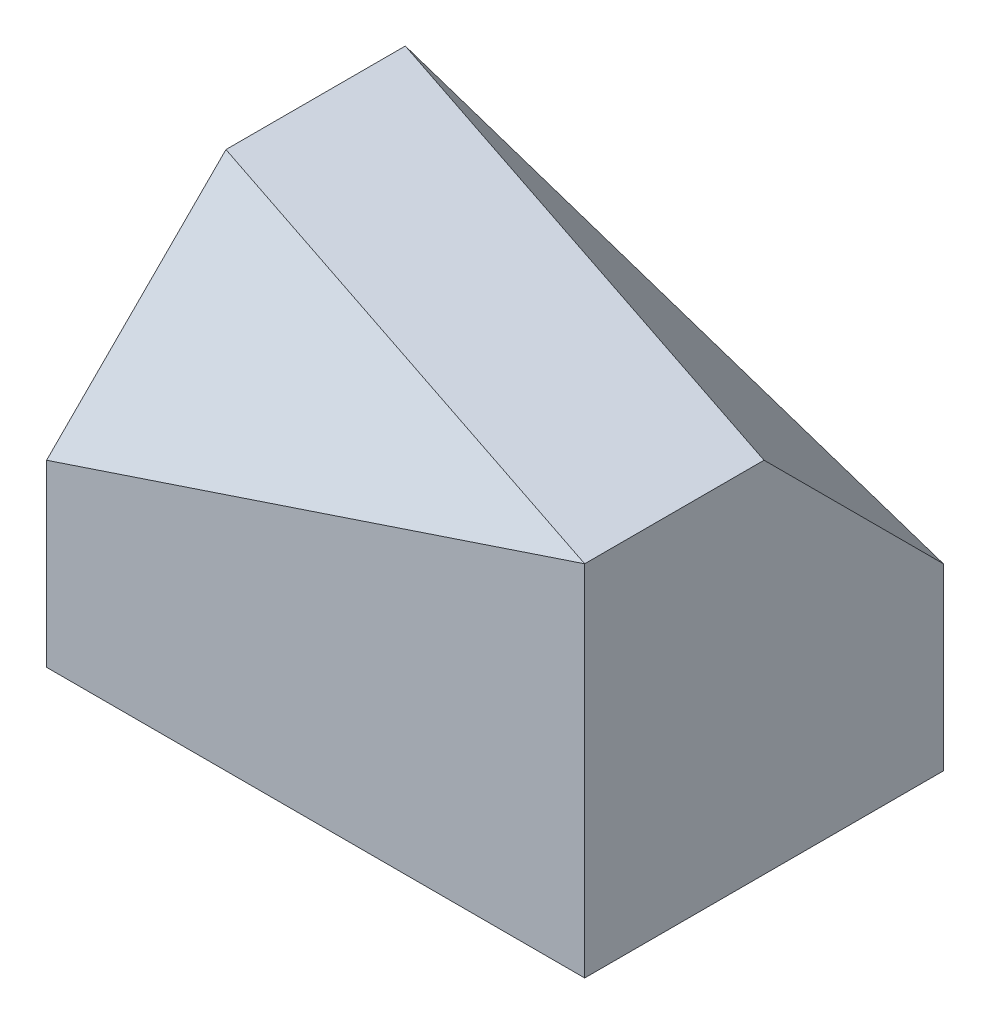
SolidWorks part; units mm, degrees
ref_plane "Front Plane" through (0, 0, 0) normal (0, 0, 1) x (1, 0, 0)
ref_plane "Top Plane" through (0, 0, 0) normal (0, 1, 0) x (1, 0, 0)
ref_plane "Right Plane" through (0, 0, 0) normal (1, 0, 0) x (0, 0, -1)
sketch "Sketch1" plane through (0, 0, 0) normal (0, 1, 0) x (1, 0, 0)
  line L0 (0, 0) -> (0, 1016)
  line L1 (0, 1016) -> (1524, 1016)
  line L2 (1524, 1016) -> (1524, 0)
  line L3 (1524, 0) -> (0, 0)
  line L4 (0, 1016) -> (1524, 508)
  line L5 (1524, 0) -> (0, 508)
  point P6 (1524, 575.0148)
  point P8 (0, 0)
  point P9 (1524, 508)
  dimension "D1" = 1524
  dimension "D2" = 1016
extrude "Boss-Extrude1" add sketch "Sketch1" along normal blind 1016 contours L5 L2 L4 L0 | L1 L4 L2 | L3 L5 L0
sketch "Sketch2" plane through (1524, 0, 0) normal (1, 0, 0) x (0, 0, -1)
  line L0 (508, 1016) -> (1016, 508)
  line L1 (1016, 1016) -> (0, 1016) construction
  line L2 (1016, 1016) -> (1016, 0) construction
ref_plane "Plane1" through (320.8421, 962.5263, -962.5263) normal (0.2294, 0.6882, -0.6882) x (-0.9733, 0.1622, -0.1622)
other "SurfaceCut1"
sketch "Sketch5" plane through (0, 0, 0) normal (-1, 0, 0) x (0, 0, 1)
  line L0 (-508, 1016) -> (0, 508)
  line L1 (0, 1016) -> (-1016, 1016) construction
  line L2 (0, 1016) -> (0, 0) construction
ref_plane "Plane2" through (-80.2105, 240.6316, 240.6316) normal (-0.2294, 0.6882, 0.6882) x (0.9733, 0.1622, 0.1622)
other "SurfaceCut2"
